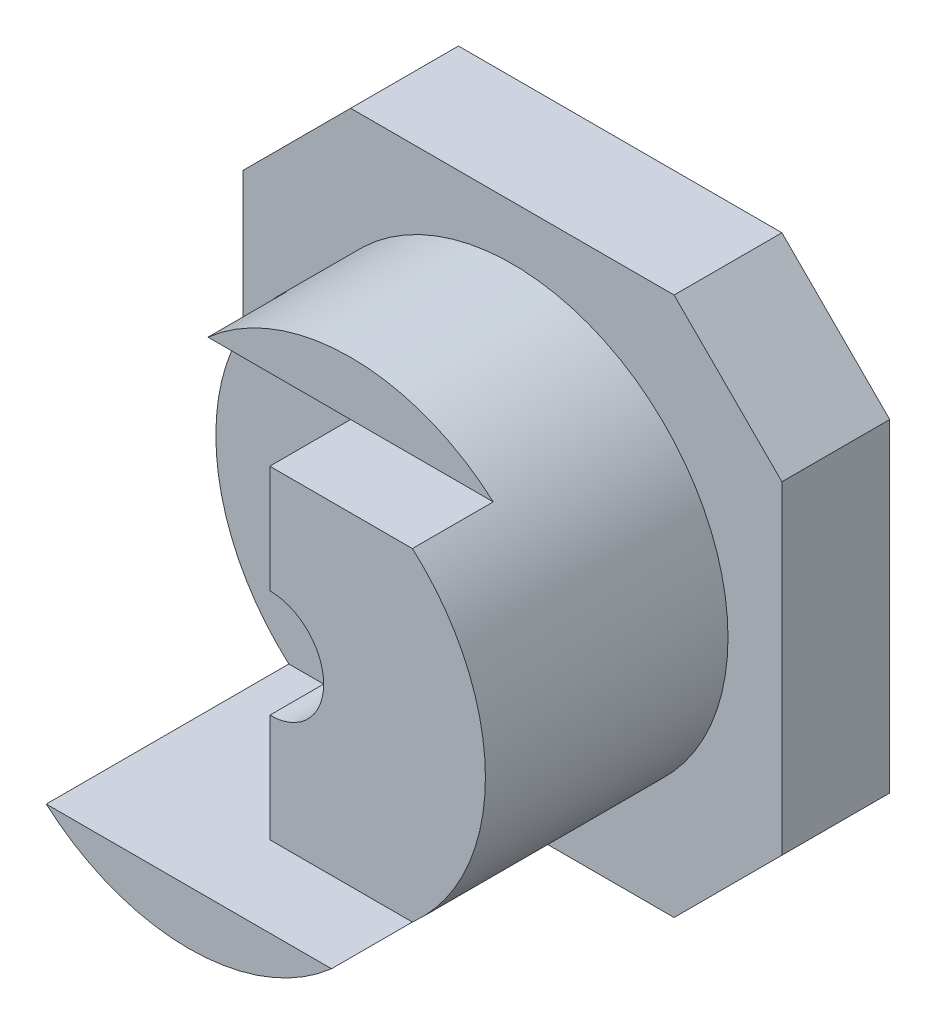
SolidWorks part; units mm, degrees
ref_plane "Front" through (0, 0, 0) normal (0, 0, 1) x (1, 0, 0)
ref_plane "Top" through (0, 0, 0) normal (0, 1, 0) x (1, 0, 0)
ref_plane "Right" through (0, 0, 0) normal (1, 0, 0) x (0, 0, -1)
sketch "Sketch1" plane through (0, 0, 0) normal (0, 0, 1) x (1, 0, 0)
  line L0 (-5, 3) -> (-3, 5)
  line L1 (-3, -5) -> (3, -5)
  line L2 (-5, -3) -> (-5, 3)
  line L3 (-3, 5) -> (3, 5)
  line L4 (5, -3) -> (5, 3)
  line L5 (-5, -5) -> (5, 5) construction
  line L6 (-5, 5) -> (5, -5) construction
  line L7 (3, 5) -> (5, 3)
  line L8 (3, -5) -> (5, -3)
  line L9 (-5, -3) -> (-3, -5)
  circle A0 centre (0, 0) radius 1
  point P0 (0, 0)
  dimension "D3" = 2
  dimension "D1" = 10
  dimension "D2" = 10
extrude "Boss-Extrude1" add sketch "Sketch1" along normal blind 2
sketch "Sketch2" plane through (0, 0, 2) normal (0, 0, 1) x (1, 0, 0)
  circle A0 centre (0, 0) radius 4
  circle A1 centre (0, 0) radius 1
  dimension "D2" = 4
  dimension "D1" = 0
extrude "Boss-Extrude2" add sketch "Sketch2" along normal blind 6
sketch "Sketch4" plane through (0, 0, 0) normal (1, 0, 0) x (0, 0, -1)
  line L0 (-8, -3) -> (-6.5, -3)
  line L1 (-8, 4) -> (-8, -4) construction
  line L2 (-6.5, -3) -> (-6.5, 3)
  line L3 (-6.5, 3) -> (-5, 3)
  line L4 (-5, 3) -> (-5, 4)
  line L5 (-5, 4) -> (-8, 4)
  line L6 (-8, 4) -> (-8, -3)
  dimension "D1" = 3
  dimension "D2" = 1
  dimension "D3" = 1.5
  dimension "D4" = 7
extrude "Cut-Extrude2" cut sketch "Sketch4" against normal mid plane 16
sketch "Sketch5" plane through (0, 0, 0) normal (1, 0, 0) x (0, 0, -1)
  line L1 (-6.5, 3) -> (-3.5, 3)
  line L2 (-6.5, 3) -> (-6.5, -3)
  line L3 (-6.5, -3) -> (-3.5, -3)
  line L4 (-3.5, 3) -> (-3.5, -3)
  dimension "D1" = 3
  dimension "D2" = 6
extrude "Cut-Extrude3" cut sketch "Sketch5" against normal blind 16
